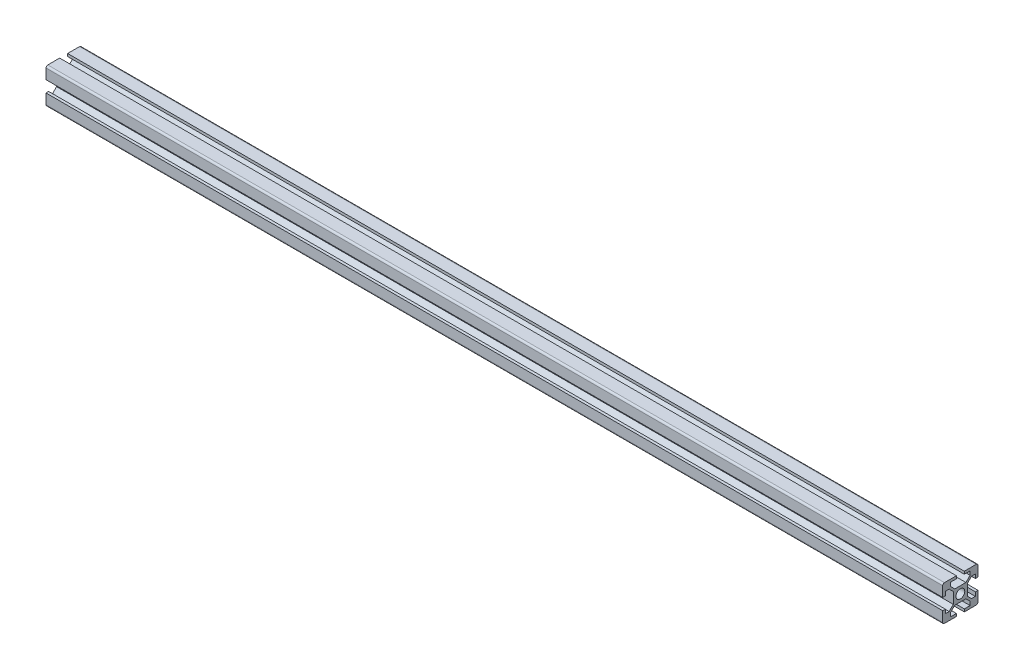
SolidWorks part; units mm, degrees
ref_plane "前视基准面" through (0, 0, 0) normal (0, 0, 1) x (1, 0, 0)
ref_plane "上视基准面" through (0, 0, 0) normal (0, 1, 0) x (1, 0, 0)
ref_plane "右视基准面" through (0, 0, 0) normal (1, 0, 0) x (0, 0, -1)
sketch3d "3D草图1"
  line L0 (0, 0, 0) -> (508, 0, 0)
other "铝型材 20 X 20 X 2(2)"
ref_plane "基准面5" through (0, 0, 0) normal (1, 0, 0) x (0, 0, -1)
sketch "草图1" plane through (0, 0, 0) normal (1, 0, 0) x (0, 0, -1)
  line L175 (-10, 9) -> (-10, 3.25)
  line L176 (-9, -10) -> (-2.25, -10)
  line L177 (-10, -3.25) -> (-10, -9)
  line L178 (-9, 10) -> (-2.25, 10)
  line L179 (-2.25, -8.5) -> (-2.25, -10)
  line L180 (-2.25, 8.5) -> (-2.25, 10)
  line L181 (-8.5, 3.25) -> (-10, 3.25)
  line L182 (-8.5, 5.5) -> (-8.5, 3.25)
  line L183 (-10, 0) -> (10, 0) construction
  line L184 (-3.1515, -4) -> (3.1515, -4)
  line L185 (-3.1515, 4) -> (3.1515, 4)
  line L186 (-8.5, 5.5) -> (-6.3485, 5.5)
  line L187 (0, -10) -> (0, 10) construction
  line L188 (-4, -3.1515) -> (-4, 3.1515)
  line L189 (-8.5, -3.25) -> (-10, -3.25)
  line L190 (-8.5, -5.5) -> (-8.5, -3.25)
  line L191 (-8.5, -5.5) -> (-6.3485, -5.5)
  line L192 (-4, 3.1515) -> (-6.3485, 5.5)
  line L193 (-4, -3.1515) -> (-6.3485, -5.5)
  line L194 (-5.5, -8.5) -> (-2.25, -8.5)
  line L195 (-5.5, -8.5) -> (-5.5, -6.3485)
  line L196 (-3.1515, -4) -> (-5.5, -6.3485)
  line L197 (-5.5, 8.5) -> (-2.25, 8.5)
  line L198 (-5.5, 8.5) -> (-5.5, 6.3485)
  line L199 (-3.1515, 4) -> (-5.5, 6.3485)
  line L200 (10, 9) -> (10, 3.25)
  line L201 (9, -10) -> (2.25, -10)
  line L202 (10, -3.25) -> (10, -9)
  line L203 (9, 10) -> (2.25, 10)
  line L204 (2.25, -8.5) -> (2.25, -10)
  line L205 (2.25, 8.5) -> (2.25, 10)
  line L206 (8.5, 3.25) -> (10, 3.25)
  line L207 (8.5, 5.5) -> (8.5, 3.25)
  line L208 (8.5, 5.5) -> (6.3485, 5.5)
  line L209 (4, -3.1515) -> (4, 3.1515)
  line L210 (8.5, -3.25) -> (10, -3.25)
  line L211 (8.5, -5.5) -> (8.5, -3.25)
  line L212 (8.5, -5.5) -> (6.3485, -5.5)
  line L213 (4, 3.1515) -> (6.3485, 5.5)
  line L214 (4, -3.1515) -> (6.3485, -5.5)
  line L215 (5.5, -8.5) -> (2.25, -8.5)
  line L216 (5.5, -8.5) -> (5.5, -6.3485)
  line L217 (3.1515, -4) -> (5.5, -6.3485)
  line L218 (5.5, 8.5) -> (2.25, 8.5)
  line L219 (5.5, 8.5) -> (5.5, 6.3485)
  line L220 (3.1515, 4) -> (5.5, 6.3485)
  arc A28 (-10, -9) -> (-9, -10) centre (-9, -9) ccw
  arc A29 (-9, 10) -> (-10, 9) centre (-9, 9) ccw
  circle A30 centre (0, 0) radius 2.5
  arc A31 (9, -10) -> (10, -9) centre (9, -9) ccw
  arc A32 (10, 9) -> (9, 10) centre (9, 9) ccw
  point P0 (0, 0)
